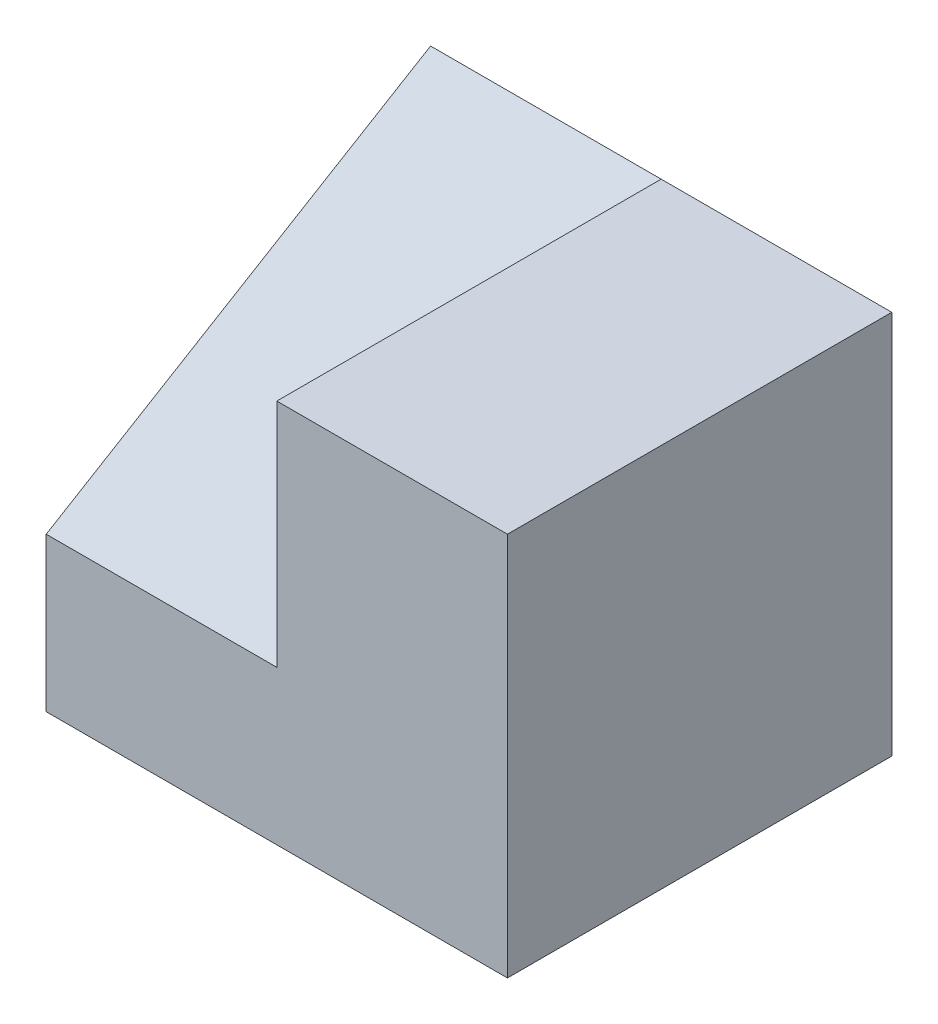
SolidWorks part; units mm, degrees
ref_plane "Front Plane" through (0, 0, 0) normal (0, 0, 1) x (1, 0, 0)
ref_plane "Top Plane" through (0, 0, 0) normal (0, 1, 0) x (1, 0, 0)
ref_plane "Right Plane" through (0, 0, 0) normal (1, 0, 0) x (0, 0, -1)
sketch "Sketch1" plane through (0, 0, 0) normal (0, 0, 1) x (1, 0, 0)
  line L0 (-30, 10) -> (-15, 10)
  line L1 (-15, 10) -> (-15, 25)
  line L2 (-15, 25) -> (0, 25)
  line L3 (0, 25) -> (0, 0)
  line L4 (0, 0) -> (-30, 0)
  line L5 (-30, 0) -> (-30, 10)
  dimension "D1" = 15
  dimension "D2" = 25
  dimension "D3" = 30
  dimension "D4" = 10
extrude "Boss-Extrude1" add sketch "Sketch1" along normal blind 25
sketch "Sketch2" plane through (-15, 0, 0) normal (-1, 0, 0) x (0, 0, 1)
  line L0 (0, 25) -> (25, 10)
  line L1 (25, 10) -> (0, 10)
  line L2 (0, 10) -> (0, 25)
extrude "Boss-Extrude2" add sketch "Sketch2" along normal blind 15
sketch "Sketch3" plane through (0, 0, 0) normal (0, 0, -1) x (-1, 0, 0)
  line L0 (15, 0) -> (15, 15)
  line L1 (30, 0) -> (0, 0) construction
  line L2 (15, 15) -> (30, 15)
  line L3 (30, 25) -> (30, 0) construction
  line L4 (30, 15) -> (30, 0)
  line L5 (30, 0) -> (15, 0)
  dimension "D1" = 15
  dimension "D2" = 15
extrude "Cut-Extrude1" cut sketch "Sketch3" against normal blind 15
